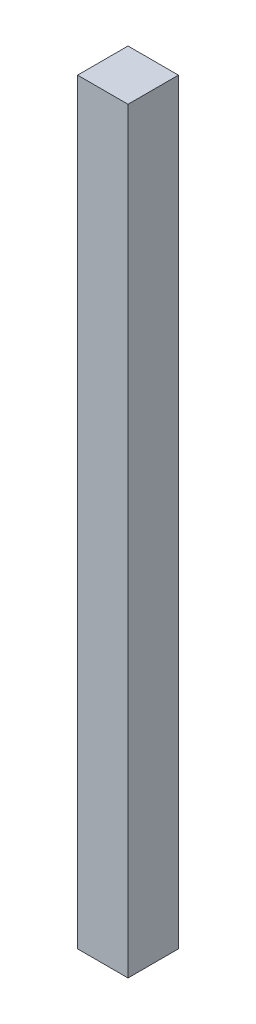
SolidWorks part; units mm, degrees
ref_plane "前视基准面" through (0, 0, 0) normal (0, 0, 1) x (1, 0, 0)
ref_plane "上视基准面" through (0, 0, 0) normal (0, 1, 0) x (1, 0, 0)
ref_plane "右视基准面" through (0, 0, 0) normal (1, 0, 0) x (0, 0, -1)
sketch "草图1" plane through (0, 0, 0) normal (0, 1, 0) x (1, 0, 0)
  line L1 (100, -100) -> (-100, -100)
  line L2 (100, -100) -> (100, 100)
  line L3 (100, 100) -> (-100, 100)
  line L4 (-100, -100) -> (-100, 100)
  line L5 (100, -100) -> (-100, 100) construction
  line L6 (100, 100) -> (-100, -100) construction
  point P0 (0, 0)
extrude "凸台-拉伸2" add sketch "草图1" against normal blind 3000
